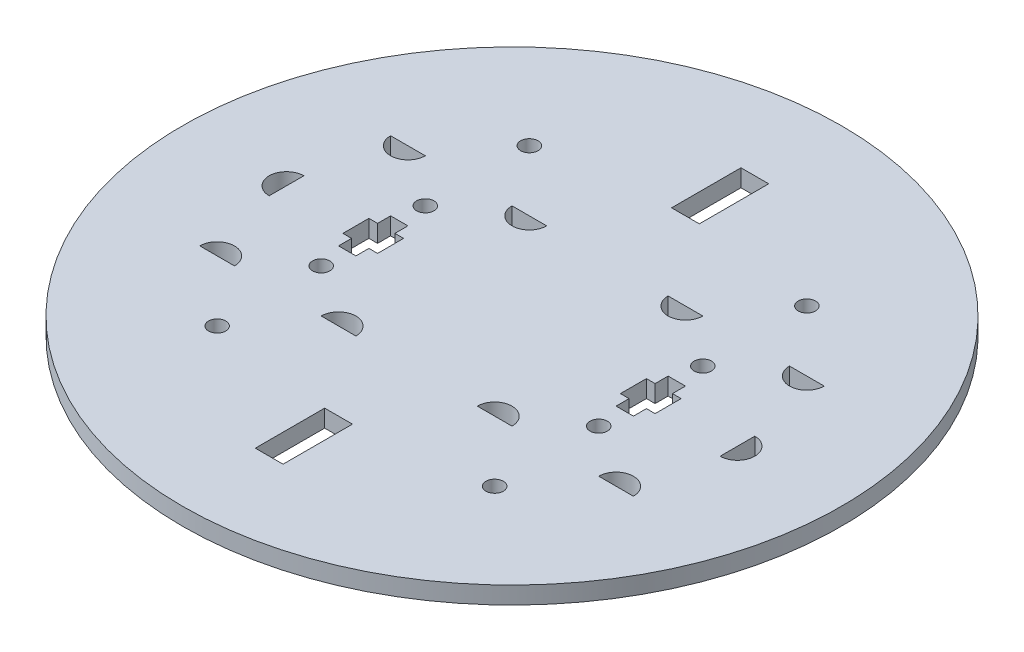
SolidWorks part; units mm, degrees
material "Ceramic Porcelain"
ref_plane "Front Plane" through (0, 0, 0) normal (0, 0, 1) x (1, 0, 0)
ref_plane "Top Plane" through (0, 0, 0) normal (0, 1, 0) x (1, 0, 0)
ref_plane "Right Plane" through (0, 0, 0) normal (1, 0, 0) x (0, 0, -1)
ref_plane "Plane1" through (0, 0, 0) normal (0, 1, 0) x (1, 0, 0)
sketch "Sketch1" plane through (0, 0, 0) normal (0, 1, 0) x (1, 0, 0)
  line L0 (-0.4, 7) -> (0.4, 7)
  line L1 (0.4, 7) -> (0.4, 5)
  line L2 (0.4, 5) -> (-0.4, 5)
  line L3 (-0.4, 5) -> (-0.4, 7)
  line L4 (-0.4, -5) -> (0.4, -5)
  line L5 (0.4, -5) -> (0.4, -7)
  line L6 (0.4, -7) -> (-0.4, -7)
  line L7 (-0.4, -7) -> (-0.4, -5)
  circle A0 centre (-4, 4.5) radius 0.25
  circle A1 centre (4, 4.5) radius 0.25
  circle A2 centre (4, -4.5) radius 0.25
  circle A3 centre (-4, -4.5) radius 0.25
  circle A4 centre (0, 0) radius 9.5
extrude "Extrude1" add sketch "Sketch1" along normal blind 0.5
ref_plane "Plane2" through (0, 0, 0) normal (0, 1, 0) x (1, 0, 0)
sketch "Sketch2" plane through (0, 0, 0) normal (0, 1, 0) x (1, 0, 0)
  line L0 (3.75, 0.75) -> (4.25, 0.75)
  line L1 (4.5, 0.375) -> (4.5, -0.375)
  line L2 (4.25, -0.75) -> (3.75, -0.75)
  line L3 (3.5, -0.375) -> (3.5, 0.375)
  line L4 (4.25, 0.75) -> (4.25, 0.375)
  line L5 (4.25, 0.375) -> (4.5, 0.375)
  line L6 (3.75, 0.75) -> (3.75, 0.375)
  line L7 (3.75, 0.375) -> (3.5, 0.375)
  line L8 (4.25, -0.75) -> (4.25, -0.375)
  line L9 (4.25, -0.375) -> (4.5, -0.375)
  line L10 (3.75, -0.75) -> (3.75, -0.375)
  line L11 (3.75, -0.375) -> (3.5, -0.375)
  line L12 (-3.5, 0.375) -> (-3.5, -0.375)
  line L13 (-3.5, -0.375) -> (-3.75, -0.375)
  line L14 (-3.75, -0.375) -> (-3.75, -0.75)
  line L15 (-3.75, -0.75) -> (-4.25, -0.75)
  line L16 (-4.25, -0.75) -> (-4.25, -0.375)
  line L17 (-4.25, -0.375) -> (-4.5, -0.375)
  line L18 (-4.5, -0.375) -> (-4.5, 0.375)
  line L19 (-4.5, 0.375) -> (-4.25, 0.375)
  line L20 (-4.25, 0.375) -> (-4.25, 0.75)
  line L21 (-4.25, 0.75) -> (-3.75, 0.75)
  line L22 (-3.75, 0.75) -> (-3.75, 0.375)
  line L23 (-3.75, 0.375) -> (-3.5, 0.375)
  line L24 (-6.5, 0.5) -> (-6.5, -0.5)
  line L25 (6.5, 0.5) -> (6.5, -0.5)
  line L26 (-6.25, 2.75) -> (-5.25, 2.75)
  line L27 (-2.75, 2.75) -> (-1.75, 2.75)
  line L28 (1.75, 2.75) -> (2.75, 2.75)
  line L29 (5.25, 2.75) -> (6.25, 2.75)
  line L30 (-6.25, -2.75) -> (-5.25, -2.75)
  line L31 (-2.75, -2.75) -> (-1.75, -2.75)
  line L32 (1.75, -2.75) -> (2.75, -2.75)
  line L33 (5.25, -2.75) -> (6.25, -2.75)
  circle A0 centre (4, 1.5) radius 0.25
  circle A1 centre (4, -1.5) radius 0.25
  circle A2 centre (-4, 1.5) radius 0.25
  circle A3 centre (-4, -1.5) radius 0.25
  arc A4 (-6.5, 0.5) -> (-6.5, -0.5) centre (-6.5, 0) ccw
  arc A5 (6.5, -0.5) -> (6.5, 0.5) centre (6.5, 0) ccw
  arc A6 (5.25, 2.75) -> (6.25, 2.75) centre (5.75, 2.75) ccw
  arc A7 (1.75, 2.75) -> (2.75, 2.75) centre (2.25, 2.75) ccw
  arc A8 (-2.75, 2.75) -> (-1.75, 2.75) centre (-2.25, 2.75) ccw
  arc A9 (-6.25, 2.75) -> (-5.25, 2.75) centre (-5.75, 2.75) ccw
  arc A10 (6.25, -2.75) -> (5.25, -2.75) centre (5.75, -2.75) ccw
  arc A11 (2.75, -2.75) -> (1.75, -2.75) centre (2.25, -2.75) ccw
  arc A12 (-1.75, -2.75) -> (-2.75, -2.75) centre (-2.25, -2.75) ccw
  arc A13 (-5.25, -2.75) -> (-6.25, -2.75) centre (-5.75, -2.75) ccw
  dimension "D1" = 1.5
  dimension "D2" = 1.5
extrude "Extrude2" cut sketch "Sketch2" along normal through all
